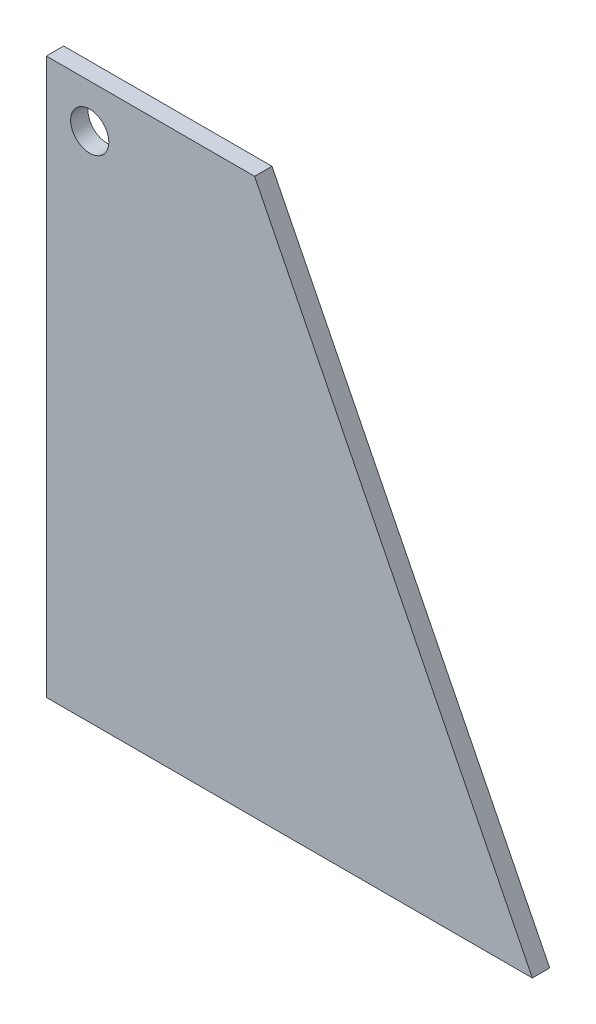
SolidWorks part; units mm, degrees
ref_plane "Front Plane" through (0, 0, 0) normal (0, 0, 1) x (1, 0, 0)
ref_plane "Top Plane" through (0, 0, 0) normal (0, 1, 0) x (1, 0, 0)
ref_plane "Right Plane" through (0, 0, 0) normal (1, 0, 0) x (0, 0, -1)
sketch "Sketch1" plane through (0, 0, 0) normal (0, 0, 1) x (1, 0, 0)
  line L0 (-88.9, 101.6) -> (-88.9, -101.6)
  line L3 (-88.9, 101.6) -> (-12.7, 101.6)
  line L8 (-88.9, -101.6) -> (88.9, -101.6)
  line L11 (-12.7, 101.6) -> (88.9, -101.6)
  circle A0 centre (-73.025, 85.725) radius 6.985
  point P0 (0, 0)
  point P8 (0, -101.6)
  point P10 (-88.9, 0)
  dimension "D3" = 13.97
  dimension "D5" = 203.2
  dimension "D6" = 15.875
  dimension "D1" = 76.2
  dimension "D4" = 15.875
  dimension "D7" = 177.8
extrude "Boss-Extrude1" add sketch "Sketch1" along normal mid plane 6.35
